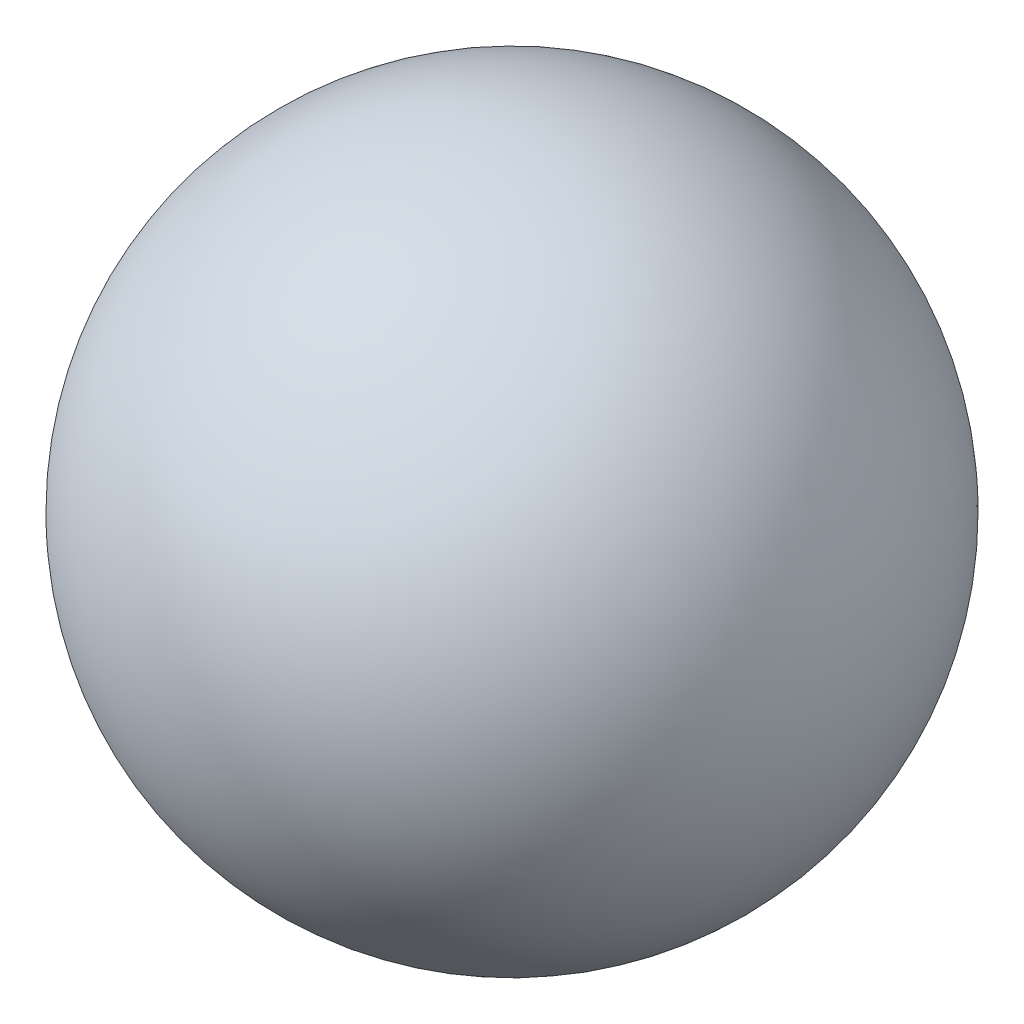
SolidWorks part; units mm, degrees
ref_plane "Front Plane" through (0, 0, 0) normal (0, 0, 1) x (1, 0, 0)
ref_plane "Top Plane" through (0, 0, 0) normal (0, 1, 0) x (1, 0, 0)
ref_plane "Right Plane" through (0, 0, 0) normal (1, 0, 0) x (0, 0, -1)
sketch "Sketch2" plane through (0, 0, 0) normal (0, 1, 0) x (1, 0, 0)
  line L0 (0, 0) -> (10.3152, 12.2309)
  arc A0 (0, 0) -> (10.3152, 12.2309) centre (5.1576, 6.1155) cw
  dimension "D1" = 16
  dimension "D2" = 5.1576
revolve "Revolve1" add sketch "Sketch2" angle 360 about L0
